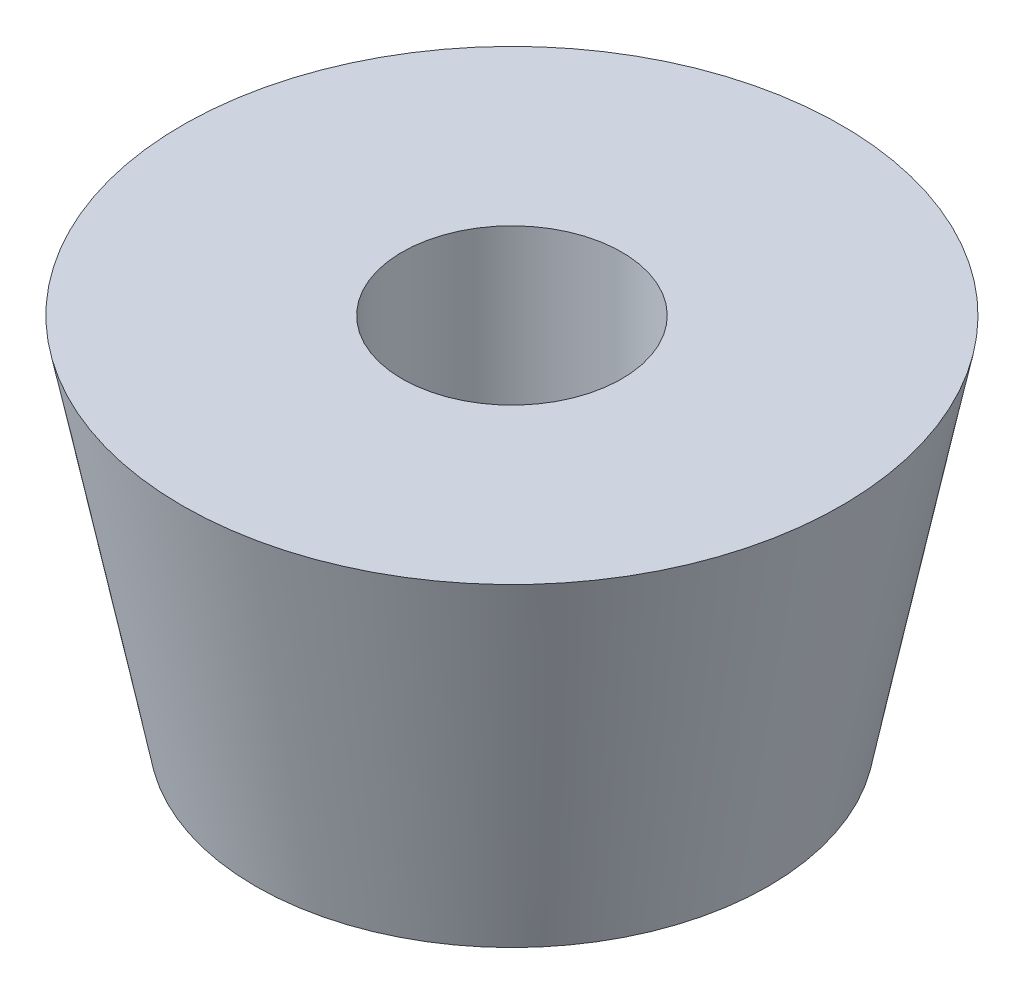
SolidWorks part; units mm, degrees
ref_plane "Front Plane" through (0, 0, 0) normal (0, 0, 1) x (1, 0, 0)
ref_plane "Top Plane" through (0, 0, 0) normal (0, 1, 0) x (1, 0, 0)
ref_plane "Right Plane" through (0, 0, 0) normal (1, 0, 0) x (0, 0, -1)
sketch "Sketch1" plane through (0, 0, 0) normal (1, 0, 0) x (0, 0, -1)
  line L0 (1.5, 0) -> (1.5, -5)
  line L1 (1.5, -5) -> (3.5, -5)
  line L2 (3.5, -5) -> (4.5, 0)
  line L3 (4.5, 0) -> (1.5, 0)
  line L4 (0, 0) -> (0, -5.9367) construction
  dimension "D1" = 5
  dimension "D2" = 3
  dimension "D3" = 2
  dimension "D4" = 1.5
revolve "Revolve1" add sketch "Sketch1" angle 360 about L4
